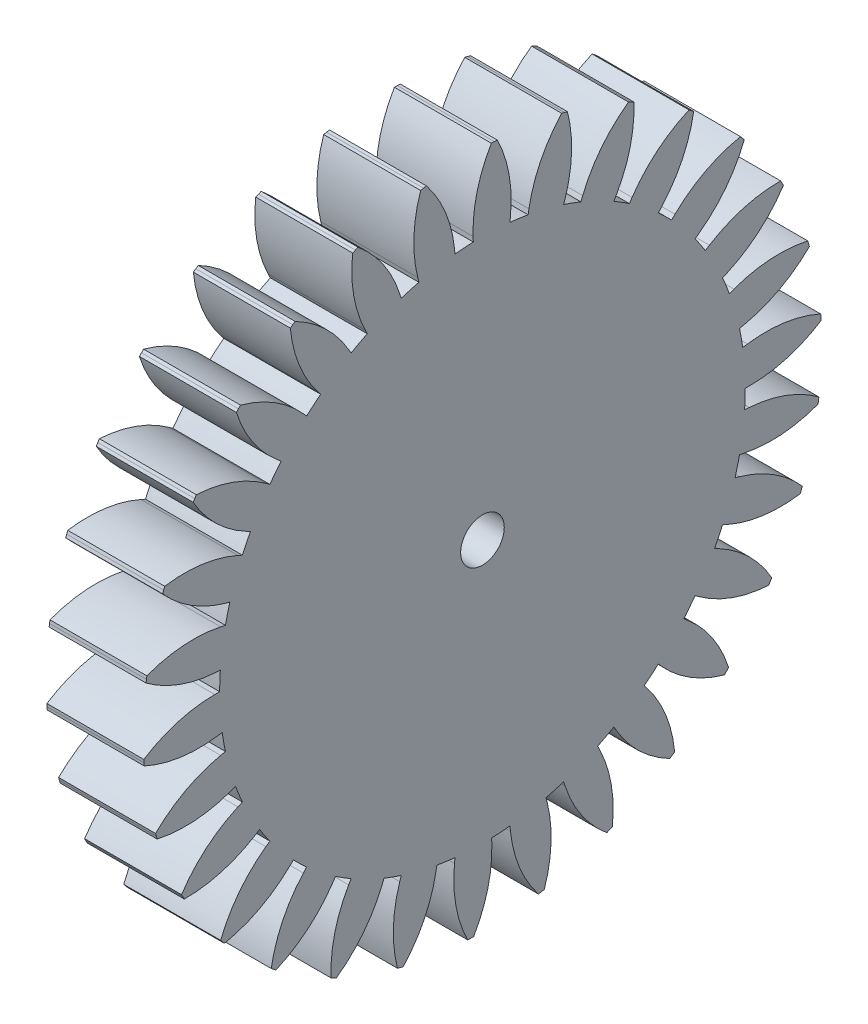
SolidWorks part; units mm, degrees
ref_plane "Front Plane" through (0, 0, 0) normal (0, 0, 1) x (1, 0, 0)
ref_plane "Top Plane" through (0, 0, 0) normal (0, 1, 0) x (1, 0, 0)
ref_plane "Right Plane" through (0, 0, 0) normal (1, 0, 0) x (0, 0, -1)
sketch "Sketch1" plane through (0, 0, 0) normal (1, 0, 0) x (0, 0, -1)
  line L0 (0, 0) -> (35, 0) construction
  line L1 (0, 0) -> (34.9347, 2.1367) construction
  line L2 (0, 0) -> (34.9147, 2.4415) construction
  line L3 (0, 0) -> (34.8921, 2.7461) construction
  line L4 (0, 0) -> (34.4683, 6.0777) construction
  line L5 (27.1081, 0) -> (27.6081, 0)
  line L6 (34.9347, 2.1367) -> (34.9147, 2.4415)
  line L7 (34.8921, 2.7461) -> (34.9147, 2.4415)
  line L8 (26.8442, 3.7727) -> (27.3394, 3.8423)
  line L9 (26.5157, -5.6361) -> (27.0048, -5.74)
  line L10 (34.6156, -5.1733) -> (34.6594, -4.8711)
  line L11 (34.7006, -4.5684) -> (34.6594, -4.8711)
  line L12 (27.042, -1.891) -> (27.5408, -1.9258)
  line L13 (0, 0) -> (34.6594, -4.8711) construction
  line L14 (24.7644, -11.0258) -> (25.2212, -11.2292)
  line L15 (32.7835, -12.2573) -> (32.8892, -11.9707)
  line L16 (32.9925, -11.6832) -> (32.8892, -11.9707)
  line L17 (26.0579, -7.472) -> (26.5386, -7.6098)
  line L18 (0, 0) -> (32.8892, -11.9707) construction
  line L19 (21.9309, -15.9337) -> (22.3354, -16.2276)
  line L20 (29.5187, -18.8055) -> (29.6817, -18.5472)
  line L21 (29.8424, -18.2874) -> (29.6817, -18.5472)
  line L22 (23.935, -12.7265) -> (24.3765, -12.9612)
  line L23 (0, 0) -> (29.6817, -18.5472) construction
  line L24 (18.1388, -20.1452) -> (18.4734, -20.5168)
  line L25 (24.9638, -24.5318) -> (25.1769, -24.313)
  line L26 (25.3881, -24.0924) -> (25.1769, -24.313)
  line L27 (20.766, -17.4247) -> (21.149, -17.7461)
  line L28 (0, 0) -> (25.1769, -24.313) construction
  line L29 (13.554, -23.4763) -> (13.804, -23.9093)
  line L30 (19.3178, -29.186) -> (19.5718, -29.0163)
  line L31 (19.8242, -28.8444) -> (19.5718, -29.0163)
  line L32 (16.6894, -21.3614) -> (16.9972, -21.7555)
  line L33 (0, 0) -> (19.5718, -29.0163) construction
  line L34 (8.3769, -25.7813) -> (8.5314, -26.2568)
  line L35 (12.8275, -32.5646) -> (13.1112, -32.4514)
  line L36 (13.3939, -32.3358) -> (13.1112, -32.4514)
  line L37 (11.8834, -24.3646) -> (12.1026, -24.814)
  line L38 (0, 0) -> (13.1112, -32.4514) construction
  line L39 (2.8336, -26.9596) -> (2.8858, -27.4568)
  line L40 (5.7767, -34.52) -> (6.0777, -34.4683)
  line L41 (6.3782, -34.4139) -> (6.0777, -34.4683)
  line L42 (6.558, -26.3028) -> (6.679, -26.788)
  line L43 (0, 0) -> (6.0777, -34.4683) construction
  line L44 (-2.8336, -26.9596) -> (-2.8858, -27.4568)
  line L45 (-1.5267, -34.9667) -> (-1.2215, -34.9787)
  line L46 (-0.9162, -34.988) -> (-1.2215, -34.9787)
  line L47 (0.9461, -27.0915) -> (0.9635, -27.5912)
  line L48 (0, 0) -> (-1.2215, -34.9787) construction
  line L49 (-8.3769, -25.7813) -> (-8.5314, -26.2568)
  line L50 (-8.7633, -33.8852) -> (-8.4673, -33.9604)
  line L51 (-8.1706, -34.0329) -> (-8.4673, -33.9604)
  line L52 (-4.7073, -26.6962) -> (-4.7941, -27.1886)
  line L53 (0, 0) -> (-8.4673, -33.9604) construction
  line L54 (-13.554, -23.4763) -> (-13.804, -23.9093)
  line L55 (-15.6169, -31.3227) -> (-15.343, -31.4578)
  line L56 (-15.0679, -31.5905) -> (-15.343, -31.4578)
  line L57 (-10.1549, -25.1342) -> (-10.3422, -25.5978)
  line L58 (0, 0) -> (-15.343, -31.4578) construction
  line L59 (-18.1388, -20.1452) -> (-18.4734, -20.5168)
  line L60 (-21.788, -27.3913) -> (-21.5482, -27.5804)
  line L61 (-21.3067, -27.7674) -> (-21.5482, -27.5804)
  line L62 (-15.1586, -22.4736) -> (-15.4382, -22.8881)
  line L63 (0, 0) -> (-21.5482, -27.5804) construction
  line L64 (-21.9309, -15.9337) -> (-22.3354, -16.2276)
  line L65 (-27.0069, -22.2627) -> (-26.8116, -22.4976)
  line L66 (-26.6142, -22.7307) -> (-26.8116, -22.4976)
  line L67 (-19.4999, -18.8308) -> (-19.8596, -19.1782)
  line L68 (0, 0) -> (-26.8116, -22.4976) construction
  line L69 (-24.7644, -11.0258) -> (-25.2212, -11.2292)
  line L70 (-31.0454, -16.1612) -> (-30.9032, -16.4315)
  line L71 (-30.7586, -16.7006) -> (-30.9032, -16.4315)
  line L72 (-22.9889, -14.3651) -> (-23.413, -14.63)
  line L73 (0, 0) -> (-30.9032, -16.4315) construction
  line L74 (-26.5157, -5.6361) -> (-27.0048, -5.74)
  line L75 (-33.7271, -9.3533) -> (-33.6442, -9.6473)
  line L76 (-33.5587, -9.9405) -> (-33.6442, -9.6473)
  line L77 (-25.4732, -9.2715) -> (-25.9431, -9.4425)
  line L78 (0, 0) -> (-33.6442, -9.6473) construction
  line L79 (-27.1081, 0) -> (-27.6081, 0)
  line L80 (-34.9347, -2.1367) -> (-34.9147, -2.4415)
  line L81 (-34.8921, -2.7461) -> (-34.9147, -2.4415)
  line L82 (-26.8442, -3.7727) -> (-27.3394, -3.8423)
  line L83 (0, 0) -> (-34.9147, -2.4415) construction
  line L84 (-26.5157, 5.6361) -> (-27.0048, 5.74)
  line L85 (-34.6156, 5.1733) -> (-34.6594, 4.8711)
  line L86 (-34.7006, 4.5684) -> (-34.6594, 4.8711)
  line L87 (-27.042, 1.891) -> (-27.5408, 1.9258)
  line L88 (0, 0) -> (-34.6594, 4.8711) construction
  line L89 (-24.7644, 11.0258) -> (-25.2212, 11.2292)
  line L90 (-32.7835, 12.2573) -> (-32.8892, 11.9707)
  line L91 (-32.9925, 11.6832) -> (-32.8892, 11.9707)
  line L92 (-26.0579, 7.472) -> (-26.5386, 7.6098)
  line L93 (0, 0) -> (-32.8892, 11.9707) construction
  line L94 (-21.9309, 15.9337) -> (-22.3354, 16.2276)
  line L95 (-29.5187, 18.8055) -> (-29.6817, 18.5472)
  line L96 (-29.8424, 18.2874) -> (-29.6817, 18.5472)
  line L97 (-23.935, 12.7265) -> (-24.3765, 12.9612)
  line L98 (0, 0) -> (-29.6817, 18.5472) construction
  line L99 (-18.1388, 20.1452) -> (-18.4734, 20.5168)
  line L100 (-24.9638, 24.5318) -> (-25.1769, 24.313)
  line L101 (-25.3881, 24.0924) -> (-25.1769, 24.313)
  line L102 (-20.766, 17.4247) -> (-21.149, 17.7461)
  line L103 (0, 0) -> (-25.1769, 24.313) construction
  line L104 (-13.554, 23.4763) -> (-13.804, 23.9093)
  line L105 (-19.3178, 29.186) -> (-19.5718, 29.0163)
  line L106 (-19.8242, 28.8444) -> (-19.5718, 29.0163)
  line L107 (-16.6894, 21.3614) -> (-16.9972, 21.7555)
  line L108 (0, 0) -> (-19.5718, 29.0163) construction
  line L109 (-8.3769, 25.7813) -> (-8.5314, 26.2568)
  line L110 (-12.8275, 32.5646) -> (-13.1112, 32.4514)
  line L111 (-13.3939, 32.3358) -> (-13.1112, 32.4514)
  line L112 (-11.8834, 24.3646) -> (-12.1026, 24.814)
  line L113 (0, 0) -> (-13.1112, 32.4514) construction
  line L114 (-2.8336, 26.9596) -> (-2.8858, 27.4568)
  line L115 (-5.7767, 34.52) -> (-6.0777, 34.4683)
  line L116 (-6.3782, 34.4139) -> (-6.0777, 34.4683)
  line L117 (-6.558, 26.3028) -> (-6.679, 26.788)
  line L118 (0, 0) -> (-6.0777, 34.4683) construction
  line L119 (2.8336, 26.9596) -> (2.8858, 27.4568)
  line L120 (1.5267, 34.9667) -> (1.2215, 34.9787)
  line L121 (0.9162, 34.988) -> (1.2215, 34.9787)
  line L122 (-0.9461, 27.0915) -> (-0.9635, 27.5912)
  line L123 (0, 0) -> (1.2215, 34.9787) construction
  line L124 (8.3769, 25.7813) -> (8.5314, 26.2568)
  line L125 (8.7633, 33.8852) -> (8.4673, 33.9604)
  line L126 (8.1706, 34.0329) -> (8.4673, 33.9604)
  line L127 (4.7073, 26.6962) -> (4.7941, 27.1886)
  line L128 (0, 0) -> (8.4673, 33.9604) construction
  line L129 (13.554, 23.4763) -> (13.804, 23.9093)
  line L130 (15.6169, 31.3227) -> (15.343, 31.4578)
  line L131 (15.0679, 31.5905) -> (15.343, 31.4578)
  line L132 (10.1549, 25.1342) -> (10.3422, 25.5978)
  line L133 (0, 0) -> (15.343, 31.4578) construction
  line L134 (18.1388, 20.1452) -> (18.4734, 20.5168)
  line L135 (21.788, 27.3913) -> (21.5482, 27.5804)
  line L136 (21.3067, 27.7674) -> (21.5482, 27.5804)
  line L137 (15.1586, 22.4736) -> (15.4382, 22.8881)
  line L138 (0, 0) -> (21.5482, 27.5804) construction
  line L139 (21.9309, 15.9337) -> (22.3354, 16.2276)
  line L140 (27.0069, 22.2627) -> (26.8116, 22.4976)
  line L141 (26.6142, 22.7307) -> (26.8116, 22.4976)
  line L142 (19.4999, 18.8308) -> (19.8596, 19.1782)
  line L143 (0, 0) -> (26.8116, 22.4976) construction
  line L144 (24.7644, 11.0258) -> (25.2212, 11.2292)
  line L145 (31.0454, 16.1612) -> (30.9032, 16.4315)
  line L146 (30.7586, 16.7006) -> (30.9032, 16.4315)
  line L147 (22.9889, 14.3651) -> (23.413, 14.63)
  line L148 (0, 0) -> (30.9032, 16.4315) construction
  line L149 (26.5157, 5.6361) -> (27.0048, 5.74)
  line L150 (33.7271, 9.3533) -> (33.6442, 9.6473)
  line L151 (33.5587, 9.9405) -> (33.6442, 9.6473)
  line L152 (25.4732, 9.2715) -> (25.9431, 9.4425)
  line L153 (0, 0) -> (33.6442, 9.6473) construction
  circle A0 centre (0, 0) radius 2.25
  circle A1 centre (0, 0) radius 27.1081
  circle A2 centre (0, 0) radius 35 construction
  arc A3 (27.6081, 0) -> (34.9347, 2.1367) centre (27.6081, 13.6298) ccw
  arc A4 (27.3394, 3.8423) -> (34.8921, 2.7461) centre (29.2363, -9.6548) cw
  arc A5 (27.0048, -5.74) -> (34.6156, -5.1733) centre (29.8385, 7.5919) ccw
  arc A6 (27.5408, -1.9258) -> (34.7006, -4.5684) centre (26.59, -15.5224) cw
  arc A7 (25.2212, -11.2292) -> (32.7835, -12.2573) centre (30.7649, 1.2222) ccw
  arc A8 (26.5386, -7.6098) -> (32.9925, -11.6832) centre (22.7817, -20.7116) cw
  arc A9 (22.3354, -16.2276) -> (29.5187, -18.8055) centre (30.3468, -5.2009) ccw
  arc A10 (24.3765, -12.9612) -> (29.8424, -18.2874) centre (17.9777, -24.9956) cw
  arc A11 (18.4734, -20.5168) -> (24.9638, -24.5318) centre (28.6023, -11.3967) ccw
  arc A12 (21.149, -17.7461) -> (25.3881, -24.0924) centre (12.388, -28.1871) cw
  arc A13 (13.804, -23.9093) -> (19.3178, -29.186) centre (25.6077, -17.0944) ccw
  arc A14 (16.9972, -21.7555) -> (19.8242, -28.8444) centre (6.2568, -30.1468) cw
  arc A15 (8.5314, -26.2568) -> (12.8275, -32.5646) centre (21.494, -22.045) ccw
  arc A16 (12.1026, -24.814) -> (13.3939, -32.3358) centre (-0.1478, -30.7889) cw
  arc A17 (2.8858, -27.4568) -> (5.7767, -34.52) centre (16.4409, -26.0321) ccw
  arc A18 (6.679, -26.788) -> (6.3782, -34.4139) centre (-6.5459, -30.0853) cw
  arc A19 (-2.8858, -27.4568) -> (-1.5267, -34.9667) centre (10.6693, -28.8815) ccw
  arc A20 (0.9635, -27.5912) -> (-0.9162, -34.988) centre (-12.6579, -28.0669) cw
  arc A21 (-8.5314, -26.2568) -> (-8.7633, -33.8852) centre (4.4313, -30.4687) ccw
  arc A22 (-4.7941, -27.1886) -> (-8.1706, -34.0329) centre (-18.2168, -24.8219) cw
  arc A23 (-13.804, -23.9093) -> (-15.6169, -31.3227) centre (-2.0003, -30.7242) ccw
  arc A24 (-10.3422, -25.5978) -> (-15.0679, -31.5905) centre (-22.9794, -20.492) cw
  arc A25 (-18.4734, -20.5168) -> (-21.788, -27.3913) centre (-8.3445, -29.6369) ccw
  arc A26 (-15.4382, -22.8881) -> (-21.3067, -27.7674) centre (-26.7378, -15.2665) cw
  arc A27 (-22.3354, -16.2276) -> (-27.0069, -22.2627) centre (-14.324, -27.2543) ccw
  arc A28 (-19.8596, -19.1782) -> (-26.6142, -22.7307) centre (-29.3276, -9.3737) cw
  arc A29 (-25.2212, -11.2292) -> (-31.0454, -16.1612) centre (-19.6775, -23.6806) ccw
  arc A30 (-23.413, -14.63) -> (-30.7586, -16.7006) centre (-30.6356, -3.0714) cw
  arc A31 (-27.0048, -5.74) -> (-33.7271, -9.3533) centre (-24.171, -19.0719) ccw
  arc A32 (-25.9431, -9.4425) -> (-33.5587, -9.9405) centre (-30.6047, 3.3653) cw
  arc A33 (-27.6081, 0) -> (-34.9347, -2.1367) centre (-27.6081, -13.6298) ccw
  arc A34 (-27.3394, -3.8423) -> (-34.8921, -2.7461) centre (-29.2363, 9.6548) cw
  arc A35 (-27.0048, 5.74) -> (-34.6156, 5.1733) centre (-29.8385, -7.5919) ccw
  arc A36 (-27.5408, 1.9258) -> (-34.7006, 4.5684) centre (-26.59, 15.5224) cw
  arc A37 (-25.2212, 11.2292) -> (-32.7835, 12.2573) centre (-30.7649, -1.2222) ccw
  arc A38 (-26.5386, 7.6098) -> (-32.9925, 11.6832) centre (-22.7817, 20.7116) cw
  arc A39 (-22.3354, 16.2276) -> (-29.5187, 18.8055) centre (-30.3468, 5.2009) ccw
  arc A40 (-24.3765, 12.9612) -> (-29.8424, 18.2874) centre (-17.9777, 24.9956) cw
  arc A41 (-18.4734, 20.5168) -> (-24.9638, 24.5318) centre (-28.6023, 11.3967) ccw
  arc A42 (-21.149, 17.7461) -> (-25.3881, 24.0924) centre (-12.388, 28.1871) cw
  arc A43 (-13.804, 23.9093) -> (-19.3178, 29.186) centre (-25.6077, 17.0944) ccw
  arc A44 (-16.9972, 21.7555) -> (-19.8242, 28.8444) centre (-6.2568, 30.1468) cw
  arc A45 (-8.5314, 26.2568) -> (-12.8275, 32.5646) centre (-21.494, 22.045) ccw
  arc A46 (-12.1026, 24.814) -> (-13.3939, 32.3358) centre (0.1478, 30.7889) cw
  arc A47 (-2.8858, 27.4568) -> (-5.7767, 34.52) centre (-16.4409, 26.0321) ccw
  arc A48 (-6.679, 26.788) -> (-6.3782, 34.4139) centre (6.5459, 30.0853) cw
  arc A49 (2.8858, 27.4568) -> (1.5267, 34.9667) centre (-10.6693, 28.8815) ccw
  arc A50 (-0.9635, 27.5912) -> (0.9162, 34.988) centre (12.6579, 28.0669) cw
  arc A51 (8.5314, 26.2568) -> (8.7633, 33.8852) centre (-4.4313, 30.4687) ccw
  arc A52 (4.7941, 27.1886) -> (8.1706, 34.0329) centre (18.2168, 24.8219) cw
  arc A53 (13.804, 23.9093) -> (15.6169, 31.3227) centre (2.0003, 30.7242) ccw
  arc A54 (10.3422, 25.5978) -> (15.0679, 31.5905) centre (22.9794, 20.492) cw
  arc A55 (18.4734, 20.5168) -> (21.788, 27.3913) centre (8.3445, 29.6369) ccw
  arc A56 (15.4382, 22.8881) -> (21.3067, 27.7674) centre (26.7378, 15.2665) cw
  arc A57 (22.3354, 16.2276) -> (27.0069, 22.2627) centre (14.324, 27.2543) ccw
  arc A58 (19.8596, 19.1782) -> (26.6142, 22.7307) centre (29.3276, 9.3737) cw
  arc A59 (25.2212, 11.2292) -> (31.0454, 16.1612) centre (19.6775, 23.6806) ccw
  arc A60 (23.413, 14.63) -> (30.7586, 16.7006) centre (30.6356, 3.0714) cw
  arc A61 (27.0048, 5.74) -> (33.7271, 9.3533) centre (24.171, 19.0719) ccw
  arc A62 (25.9431, 9.4425) -> (33.5587, 9.9405) centre (30.6047, -3.3653) cw
  point P10 (34.4683, 6.0777)
  point P11 (34.8921, 2.7461)
  point P12 (34.9147, 2.4415)
  point P13 (34.9347, 2.1367)
  point P14 (27.1081, 0)
  point P19 (34.9247, 2.2891)
  point P20 (34.9034, 2.5938)
  point P182 (0, 0)
  point P379 (0, 0)
  dimension "D1" = 4.5
  dimension "D3" = 70
  dimension "D4" = 4
  dimension "D5" = 4.5
  dimension "D6" = 3.5
  dimension "D7" = 35
  dimension "D9" = 0.5
  dimension "D2" = 30
extrude "Boss-Extrude1" add sketch "Sketch1" along normal blind 10 contours A1 | A14 L32 A1 L29 A13 L30 L31 | A12 L27 A1 L24 A11 L25 L26 | A54 L132 A1 L129 A53 L130 L131 | A56 L137 A1 L134 A55 L135 L136 | A58 L142 A1 L139 A57 L140 L141 | A60 L147 A1 L144 A59 L145 L146 | A62 L152 A1 L149 A61 L150 L151 | A4 L8 A1 L5 A3 L6 L7 | A6 L12 A1 L9 A5 L10 L11 | A8 L17 A1 L14 A7 L15 L16 | A10 L22 A1 L19 A9 L20 L21 | A16 L37 A1 L34 A15 L35 L36 | A18 L42 A1 L39 A17 L40 L41 | A20 L47 A1 L44 A19 L45 L46 | A22 L52 A1 L49 A21 L50 L51 | A24 L57 A1 L54 A23 L55 L56 | A26 L62 A1 L59 A25 L60 L61 | A28 L67 A1 L64 A27 L65 L66 | A30 L72 A1 L69 A29 L70 L71 | A32 L77 A1 L74 A31 L75 L76 | A34 L82 A1 L79 A33 L80 L81 | A36 L87 A1 L84 A35 L85 L86 | A38 L92 A1 L89 A37 L90 L91 | A40 L97 A1 L94 A39 L95 L96 | A42 L102 A1 L99 A41 L100 L101 | A44 L107 A1 L104 A43 L105 L106 | A46 L112 A1 L109 A45 L110 L111 | A48 L117 A1 L114 A47 L115 L116 | A50 L122 A1 L119 A49 L120 L121 | A52 L127 A1 L124 A51 L125 L126
equation "\"Gear_angle\"= 8"
equation "\"D4@Sketch1\"=\"Gear_angle\"*0.5"
equation "\"D5@Sketch1\"=\"Gear_angle\"*0.5 +0.5"
equation "\"D6@Sketch1\"=\"Gear_angle\"*0.5 -0.5"
equation "\"Gear_diameter\"= 70mm"
equation "\"Gear_tooth_height\"= 2mm"
equation "\"gear_thickeness\"=10"
equation "\"D7@Sketch1\"=\"Gear_diameter\"*0.5"
equation "\"gear_thickness\"=10"
equation "\"D1@Boss-Extrude1\"=\"gear_thickness\""
